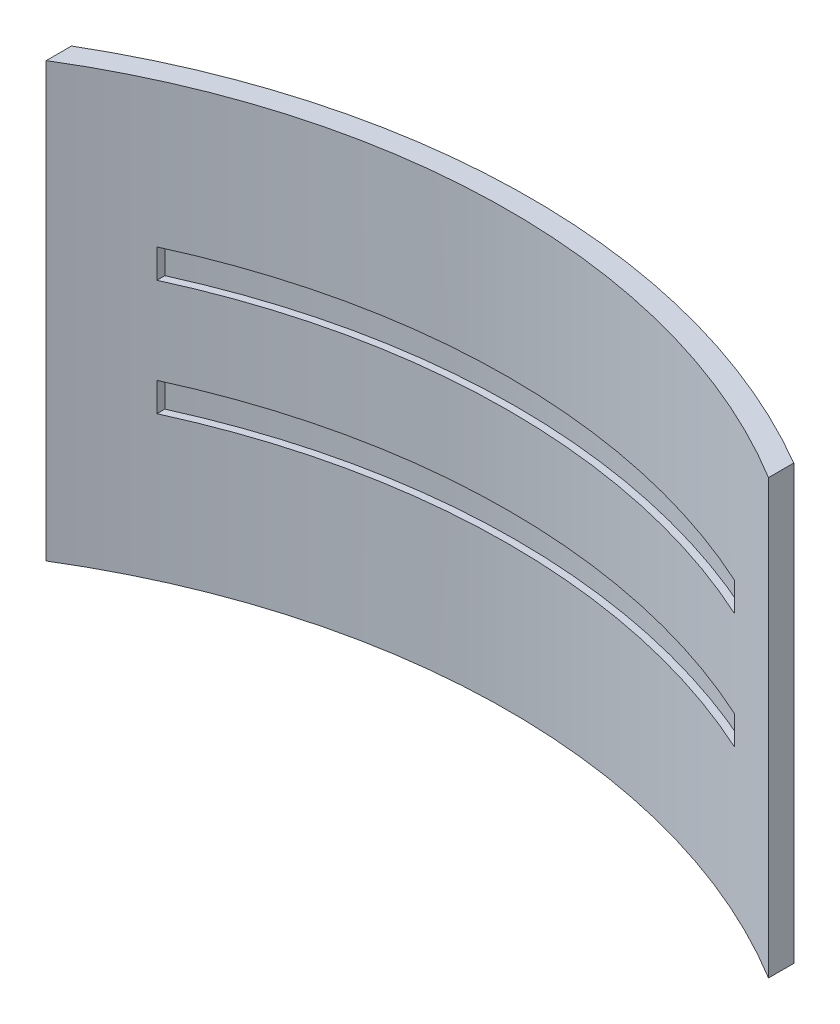
SolidWorks part; units mm, degrees
ref_plane "Front Plane" through (0, 0, 0) normal (0, 0, 1) x (1, 0, 0)
ref_plane "Top Plane" through (0, 0, 0) normal (0, 1, 0) x (1, 0, 0)
ref_plane "Right Plane" through (0, 0, 0) normal (1, 0, 0) x (0, 0, -1)
sketch "Sketch2" plane through (0, 0, 0) normal (0, 1, 0) x (1, 0, 0)
  line L0 (-25, 42.7229) -> (-25, 40.9756)
  line L1 (25, 42.7229) -> (25, 40.9756)
  line L2 (0, -54.45) -> (0, 54.45) construction
  arc A0 (25, 42.7229) -> (-25, 42.7229) centre (0, 0) ccw
  arc A1 (25, 40.9756) -> (-25, 40.9756) centre (0, 0) ccw
  dimension "D1" = 96
  dimension "D2" = 99
  dimension "D3" = 25
  dimension "D4" = 25
extrude "Boss-Extrude1" add sketch "Sketch2" along normal blind 30
ref_plane "Plane1" through (0, 0, 0) normal (0, 0, -1) x (-1, 0, 0)
sketch "Sketch3" plane through (0, 0, 0) normal (0, 0, -1) x (-1, 0, 0)
  line L7 (0, 4.6884) -> (0, -4.6884) construction
  line L12 (-20, 18) -> (20, 18)
  line L13 (-20, 18) -> (-20, 20)
  line L14 (-20, 20) -> (20, 20)
  line L15 (20, 18) -> (20, 20)
  line L16 (25, 30) -> (-25, 30) construction
  line L17 (-33.3593, 15) -> (35.7504, 15) construction
  line L18 (20, 12) -> (20, 10)
  line L19 (-20, 12) -> (-20, 10)
  line L20 (-20, 10) -> (20, 10)
  line L21 (-20, 12) -> (20, 12)
  dimension "D1" = 40
  dimension "D2" = 20
  dimension "D3" = 10
  dimension "D4" = 2
  dimension "D5" = 15
extrude "Cut-Extrude28" cut sketch "Sketch3" along normal offset from surface (44.1843 mm away) 1
ref_plane "Plane2" through (0, 0, -60) normal (0, 0, 1) x (1, 0, 0)
sketch "Sketch5" plane through (0, 0, -60) normal (0, 0, 1) x (1, 0, 0)
  line L0 (0, -4.6884) -> (0, 4.6884) construction
  line L1 (-5, 5) -> (-3, 5)
  line L2 (-5, 5) -> (-5, 25)
  line L3 (-5, 25) -> (-3, 25)
  line L4 (-3, 5) -> (-3, 25)
  line L5 (25, 30) -> (-25, 30) construction
  line L7 (5, 25) -> (3, 25)
  line L8 (3, 5) -> (3, 25)
  line L9 (5, 5) -> (5, 25)
  line L10 (5, 5) -> (3, 5)
  dimension "D1" = 2
  dimension "D2" = 3
  dimension "D3" = 20
  dimension "D4" = 5
extrude "Cut-Extrude29" cut sketch "Sketch5" along normal offset from surface (11.2558 mm away) 1
